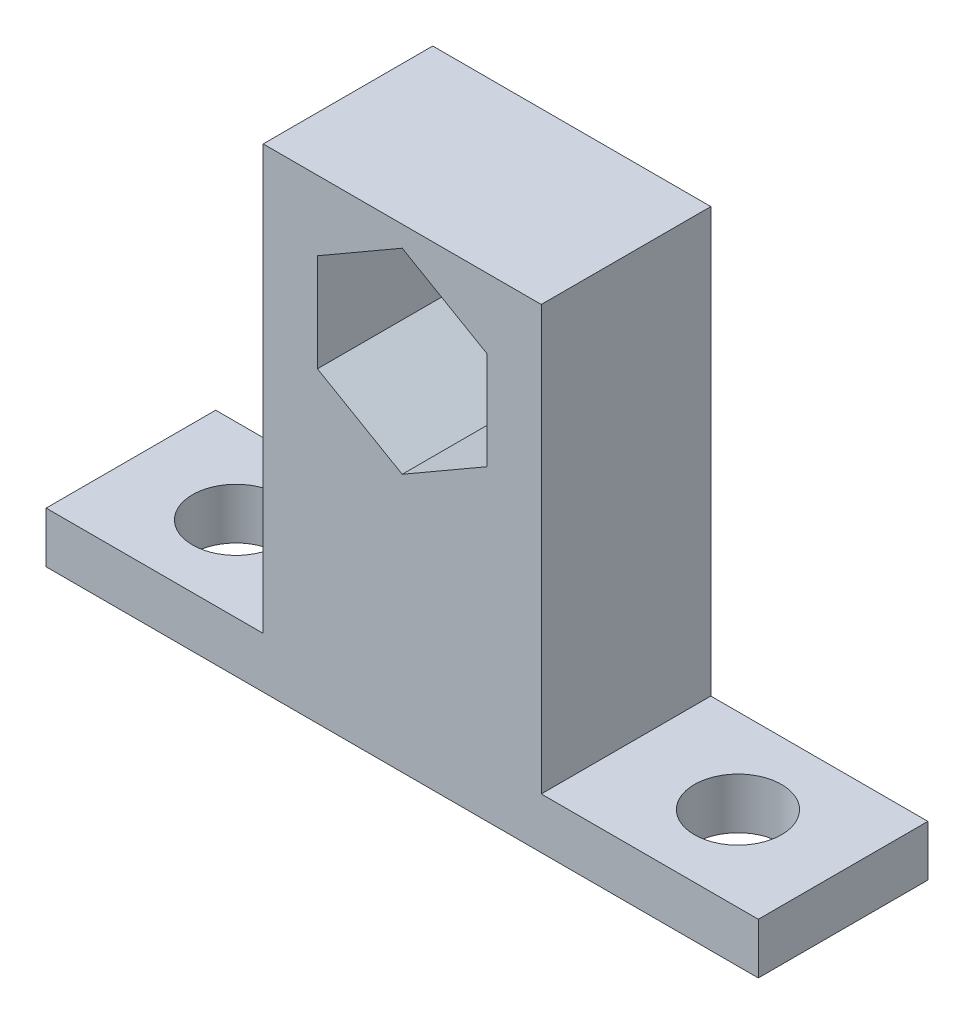
SolidWorks part; units mm, degrees
ref_plane "Front Plane" through (0, 0, 0) normal (0, 0, 1) x (1, 0, 0)
ref_plane "Top Plane" through (0, 0, 0) normal (0, 1, 0) x (1, 0, 0)
ref_plane "Right Plane" through (0, 0, 0) normal (1, 0, 0) x (0, 0, -1)
sketch "Sketch1" plane through (0, 0, 0) normal (0, 1, 0) x (1, 0, 0)
  line L1 (-35.381, 3.1139) -> (17.959, 3.1139)
  line L2 (-35.381, 3.1139) -> (-35.381, -9.5861)
  line L3 (-35.381, -9.5861) -> (17.959, -9.5861)
  line L4 (17.959, 3.1139) -> (17.959, -9.5861)
  line L5 (-19.887, 3.1139) -> (2.465, 3.1139)
  line L6 (-19.887, 3.1139) -> (-19.887, -9.5861)
  line L7 (-19.887, -9.5861) -> (2.465, -9.5861)
  line L8 (2.465, 3.1139) -> (2.465, -9.5861)
  circle A0 centre (-27.507, -3.2361) radius 3.2639
  circle A1 centre (10.085, -3.2361) radius 3.2639
  dimension "D7" = 6.5278
  dimension "D8" = 6.5278
  dimension "D1" = 12.7
  dimension "D2" = 53.34
  dimension "D3" = 7.874
  dimension "D4" = 7.874
  dimension "D5" = 6.35
  dimension "D6" = 6.35
  dimension "D9" = 7.62
  dimension "D10" = 7.62
extrude "Boss-Extrude3" add sketch "Sketch1" along normal blind 3.81 contours L6 L1 L2 L3 A0 | L8 L1 L6 L3 | L1 L8 L3 L4 A1
sketch "Sketch3" plane through (0, 3.81, 0) normal (0, 1, 0) x (1, 0, 0)
  line L0 (-35.381, -9.5861) -> (17.959, -9.5861) construction
  line L1 (-19.125, -9.5861) -> (1.703, -9.5861)
  line L2 (-19.125, -9.5861) -> (-19.125, 3.1139)
  line L3 (-19.125, 3.1139) -> (1.703, 3.1139)
  line L4 (1.703, -9.5861) -> (1.703, 3.1139)
  line L5 (-35.381, 3.1139) -> (17.959, 3.1139) construction
  circle A0 centre (-27.507, -3.2361) radius 3.2639 construction
  circle A1 centre (10.085, -3.2361) radius 3.2639 construction
  dimension "D1" = 8.382
  dimension "D2" = 8.382
extrude "Boss-Extrude4" add sketch "Sketch3" along normal blind 31.75
sketch "Sketch5" plane through (0, 0, -3.1139) normal (0, 0, -1) x (-1, 0, 0)
  line L4 (8.711, 34.0023) -> (2.361, 30.3362)
  line L5 (2.361, 30.3362) -> (2.361, 23.0038)
  line L6 (2.361, 23.0038) -> (8.711, 19.3377)
  line L7 (8.711, 19.3377) -> (15.061, 23.0038)
  line L8 (15.061, 23.0038) -> (15.061, 30.3362)
  line L9 (15.061, 30.3362) -> (8.711, 34.0023)
  dimension "D3" = 12.7
extrude "Cut-Extrude3" cut sketch "Sketch5" against normal up to next
